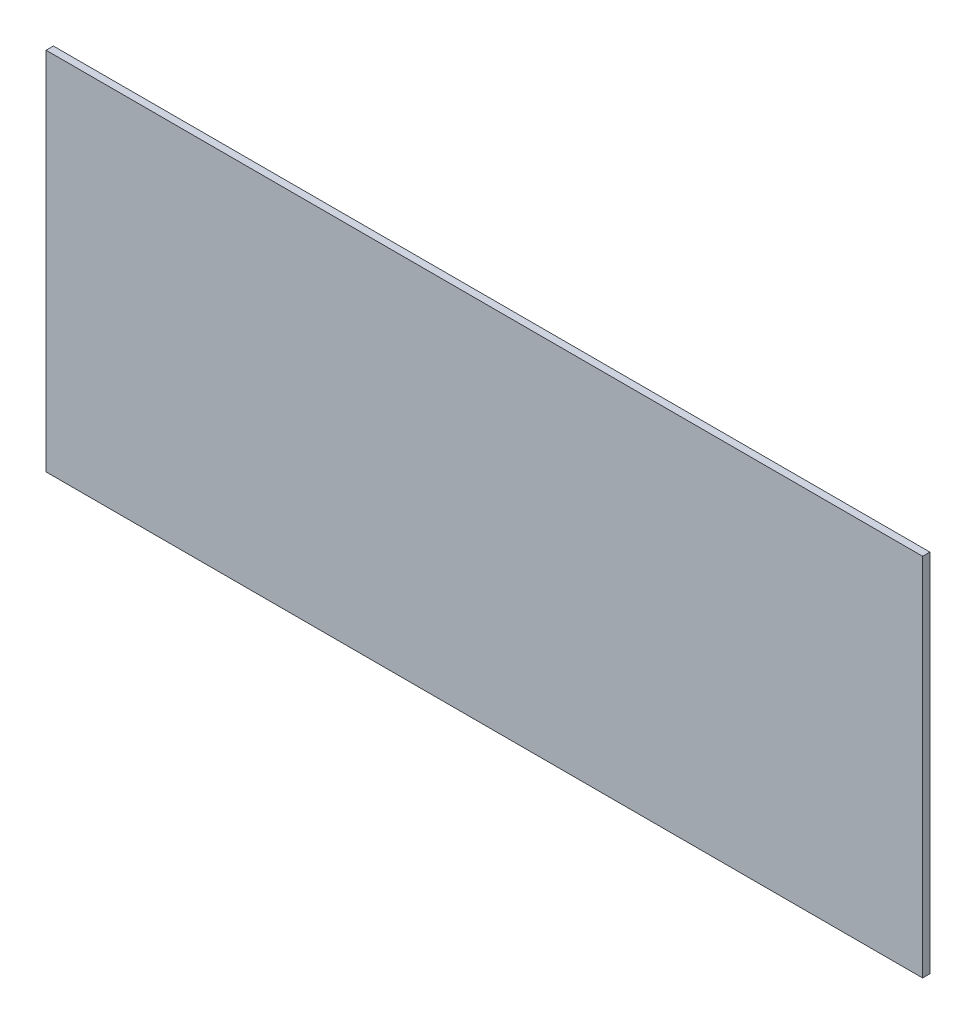
SolidWorks part; units mm, degrees
ref_plane "Front Plane" through (0, 0, 0) normal (0, 0, 1) x (1, 0, 0)
ref_plane "Top Plane" through (0, 0, 0) normal (0, 1, 0) x (1, 0, 0)
ref_plane "Right Plane" through (0, 0, 0) normal (1, 0, 0) x (0, 0, -1)
sketch "Sketch1" plane through (0, 0, 0) normal (0, 0, 1) x (1, 0, 0)
  line L0 (0, 0) -> (0, 100)
  line L1 (0, 100) -> (240, 100)
  line L2 (240, 100) -> (240, 0)
  line L3 (240, 0) -> (0, 0)
  dimension "D1" = 100
  dimension "D2" = 240
extrude "Boss-Extrude1" add sketch "Sketch1" along normal blind 2
